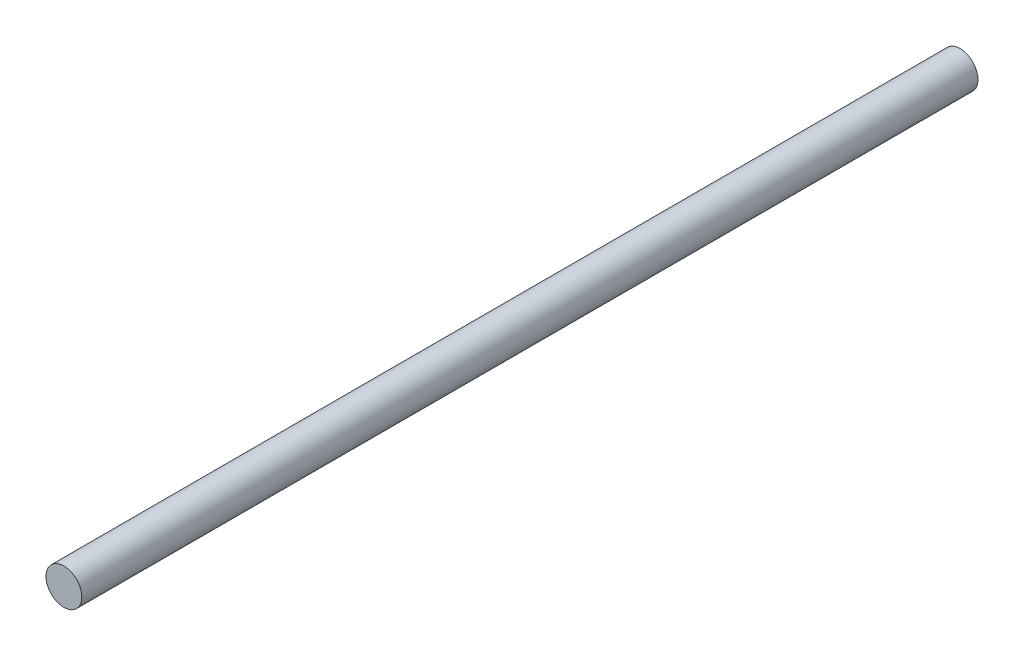
SolidWorks part; units mm, degrees
material "Liga de aço"
ref_plane "Plano frontal" through (0, 0, 0) normal (0, 0, 1) x (1, 0, 0)
ref_plane "Plano superior" through (0, 0, 0) normal (0, 1, 0) x (1, 0, 0)
ref_plane "Plano direito" through (0, 0, 0) normal (1, 0, 0) x (0, 0, -1)
sketch "Esboço1" plane through (0, 0, 0) normal (0, 0, 1) x (1, 0, 0)
  circle A0 centre (0, 0) radius 2
extrude "Ressalto-extrusão1" add sketch "Esboço1" along normal blind 100
